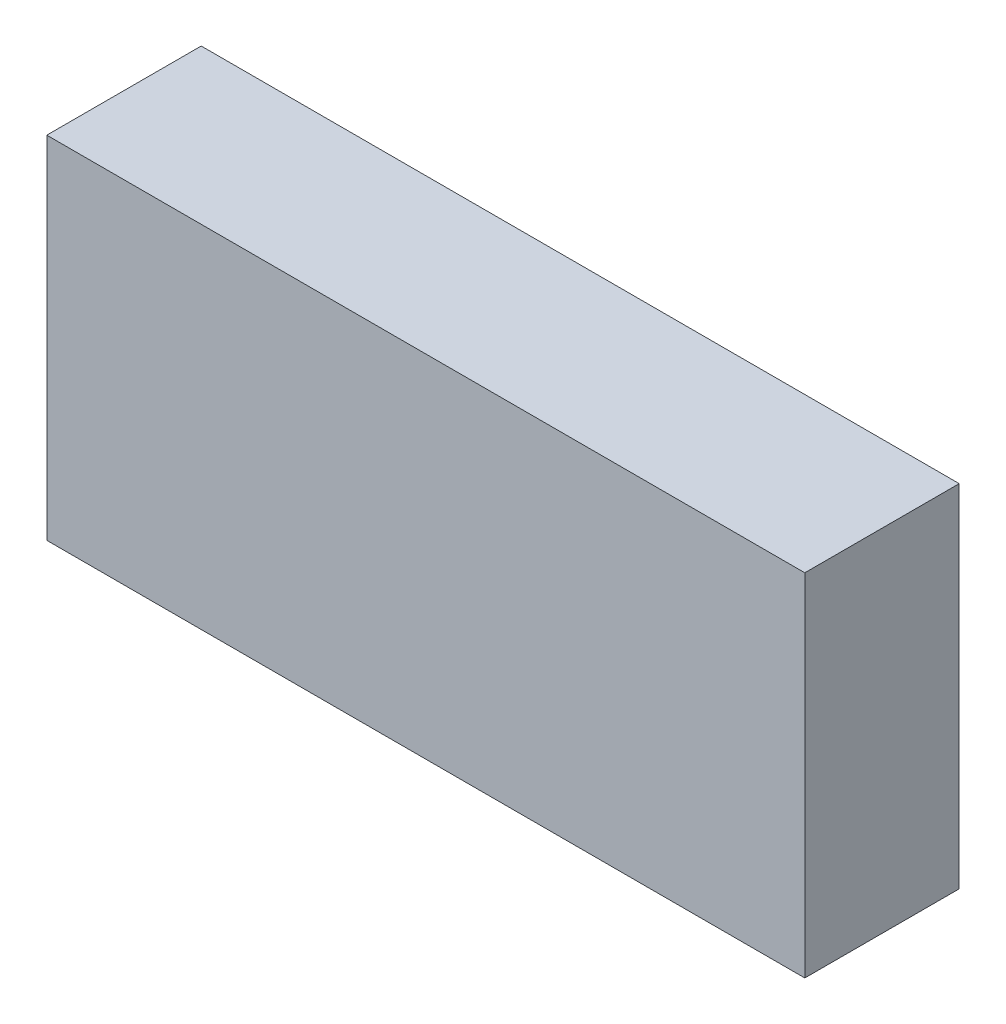
SolidWorks part; units mm, degrees
material "Plástico personalizado"
ref_plane "Plano frontal" through (0, 0, 0) normal (0, 0, 1) x (1, 0, 0)
ref_plane "Plano superior" through (0, 0, 0) normal (0, 1, 0) x (1, 0, 0)
ref_plane "Plano direito" through (0, 0, 0) normal (1, 0, 0) x (0, 0, -1)
sketch "Esboço1" plane through (0, 0, 0) normal (0, 0, 1) x (1, 0, 0)
  line L1 (0, 0) -> (54, 0)
  line L2 (0, 0) -> (0, -25)
  line L3 (0, -25) -> (54, -25)
  line L4 (54, 0) -> (54, -25)
  dimension "D1" = 54
  dimension "D2" = 25
extrude "Ressalto-extrusão1" add sketch "Esboço1" along normal blind 11
